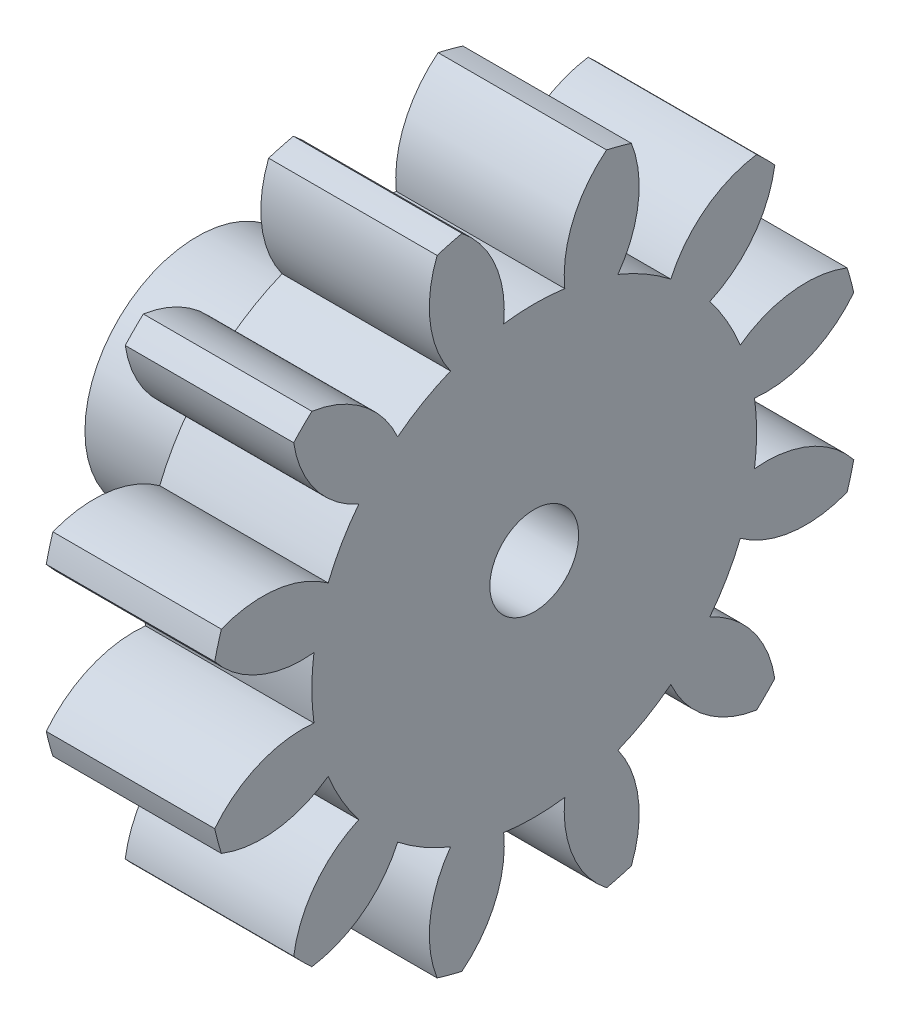
SolidWorks part; units mm, degrees
ref_plane "Plane1" through (0, 0, 0) normal (0, 0, 1) x (1, 0, 0)
ref_plane "Plane2" through (0, 0, 0) normal (0, 1, 0) x (1, 0, 0)
ref_plane "Plane3" through (0, 0, 0) normal (1, 0, 0) x (0, 0, -1)
sketch "HoldingSke" plane through (0, 0, 0) normal (0, 1, 0) x (1, 0, 0)
  line L0 (0, 0) -> (596.2788, -126.743)
  line L1 (-15, 0) -> (100, 0) construction
  line L2 (0, 0) -> (-2.1039, 2.3779)
  line L3 (0, 0) -> (-11.863, 4.5341)
  line L4 (0, 0) -> (8.4473, 1.7955)
  line L5 (0, 0) -> (-47.5972, -17.7524)
  line L6 (0, 0) -> (-3.1583, -2.1309)
  line L7 (-2.1039, 2.3779) -> (8.8308, 51.9871)
  line L8 (-76.2, 54.61) -> (-61.976, 54.61)
  line L9 (-67.7845, 28.3722) -> (-49.3413, 33.142)
  line L10 (-76.2, 71.12) -> (104.1128, 71.12)
  line L11 (0, 0) -> (-3.81, 0)
  line L12 (-76.2, 101.6) -> (-76.1573, 101.6)
  line L13 (24.9733, 27.94) -> (52.9518, 28.4284)
  line L14 (24.9733, 27.94) -> (25.0241, 27.9398)
  line L15 (24.9733, 27.94) -> (100.4021, 29.52)
  circle A0 centre (0, 0) radius 6.35
  circle A1 centre (0, 0) radius 5.0292
  circle A2 centre (0, 0) radius 38.1
  circle A3 centre (0, 0) radius 5.0038
  dimension "MHD" = 10.0584
  dimension "Hub_dia" = 76.2
  dimension "Bore" = 12.7
  dimension "MBD" = 10.0076
  dimension "Num_teeth" = 12
  dimension "Pitch" = 609.6
  dimension "Overall_len" = 50.8
  dimension "Show_teeth" = 12
  dimension "Thickness" = 3.81
  dimension "OAL" = 50.8001
  dimension "T_dim" = 14.224
  dimension "Ap" = 14.5
  dimension "H" = 19.05
  dimension "Pitch_radius" = 180.3128
  dimension "Width" = 3.81
  dimension "Backlash" = 0.0427
  dimension "Addendum_fac" = 1
  dimension "Dedendum_fac" = 1.2
  dimension "Clearance_fac" = 0.2
  dimension "Dedendum_add" = 0.0508
sketch "BasProSke" plane through (0, 0, 0) normal (0, 1, 0) x (1, 0, 0)
  line L0 (-10, 0) -> (60, 0) construction
  line L1 (0, 0) -> (0, 7.4083)
  line L2 (0, 0) -> (3.81, 0)
  line L3 (3.81, 0) -> (3.81, 7.4083)
  line L4 (3.81, 7.4083) -> (0, 7.4083)
  dimension "Thickness" = 3.81
  dimension "Diameter" = 14.8167
revolve "Base-Revolve" add sketch "BasProSke" angle 360 about L0
sketch "TooCutSke" plane through (0, 0, 0) normal (1, 0, 0) x (0, 0, -1)
  line L1 (0, 0) -> (0, 107) construction
  line L2 (0, 0) -> (-0.9034, 6.2854) construction
  line L3 (0, 0) -> (-3.2637, 12.1804) construction
  line L4 (-0.9034, 6.2854) -> (-1.6319, 6.0902) construction
  arc A0 (0.6906, 4.9816) -> (-0.6906, 4.9816) centre (0, 0) ccw
  arc A1 (1.6612, 7.2457) -> (-1.6612, 7.2457) centre (0, 0) ccw
  circle A2 centre (0, 0) radius 6.35 construction
  circle A3 centre (0, 0) radius 6.1477 construction
  arc A4 (-0.6906, 4.9816) -> (-1.6612, 7.2457) centre (-3.2176, 5.2385) ccw
  arc A5 (1.6612, 7.2457) -> (0.6906, 4.9816) centre (3.2176, 5.2385) ccw
  dimension "Root_dia" = 10.0584
  dimension "Overcut_dia" = 14.8675
  dimension "Pitch_dia" = 12.7
  dimension "Base_dia" = 12.2955
  dimension "Flank_rad" = 2.54
  dimension "Half_ang" = 15
  dimension "Half_CT" = 0.7542
extrude "ToothCut" cut sketch "TooCutSke" along normal through all
fillet "Breaks" [suppressed] radius 0.0212
fillet "RootFillets" [suppressed] radius 0.2625
pattern_circular "TeethCuts" count 12 every 30 about axis through (-10, 0, 0) along (1, 0, 0) of "ToothCut", "RootFillets", "Breaks"
sketch "HubNeaOneSke" plane through (0, 0, 0) normal (-1, 0, 0) x (0, 0, 1)
  circle A0 centre (0, 0) radius 5.0292
  dimension "Diameter" = 10.0584
extrude "HubNearOne" [suppressed] add sketch "HubNeaOneSke" along normal blind 46.9901
sketch "HubNeaBotSke" plane through (0, 0, 0) normal (-1, 0, 0) x (0, 0, 1)
  circle A0 centre (0, 0) radius 5.0292
  dimension "Diameter" = 10.0584
extrude "HubNearBoth" [suppressed] add sketch "HubNeaBotSke" along normal blind 23.495
ref_plane "FarPln" through (3.81, 0, 0) normal (1, 0, 0) x (0, 0, -1)
sketch "HubFarSke" plane through (3.81, 0, 0) normal (1, 0, 0) x (0, 0, -1)
  circle A0 centre (0, 0) radius 5.0292
  dimension "Diameter" = 10.0584
extrude "HubFar" [suppressed] add sketch "HubFarSke" along normal blind 23.495
sketch "BorSke" plane through (0, 0, 0) normal (1, 0, 0) x (0, 0, -1)
  circle A0 centre (0, 0) radius 5.0038
  dimension "Diameter" = 10.0076
extrude "Bore" cut sketch "BorSke" along normal mid plane 101.6001
sketch "KeySke" plane through (0, 0, 0) normal (1, 0, 0) x (0, 0, -1)
  line L0 (-1.5875, 0) -> (-1.5875, 9.2202)
  line L1 (-1.5875, 9.2202) -> (1.5875, 9.2202)
  line L2 (1.5875, 9.2202) -> (1.5875, 0)
  line L3 (0, 0) -> (0, 34) construction
  line L4 (-1.5875, 0) -> (1.5875, 0)
  dimension "Offset" = 9.2202
  dimension "Width" = 3.175
extrude "Keyway" [suppressed] cut sketch "KeySke" along normal mid plane 101.6001
pattern_circular "Keyway2" [suppressed] count 2 every 90 about axis through (-10, 0, 0) along (1, 0, 0)
sketch "Sketch1" plane through (0, 0, 0) normal (1, 0, 0) x (0, 0, -1)
  circle A0 centre (0, 0) radius 5.0038 construction
  circle A1 centre (0, 0) radius 5.0038
extrude "Boss-Extrude1" add sketch "Sketch1" along normal up to vertex (3.81 mm away)
sketch "Sketch2" plane through (0, 0, 0) normal (-1, 0, 0) x (0, 0, 1)
  circle A0 centre (0, 0) radius 2.54
  dimension "D1" = 5.08
extrude "Boss-Extrude2" add sketch "Sketch2" along normal blind 3.81
sketch "Sketch3" plane through (-3.81, 0, 0) normal (-1, 0, 0) x (0, 0, 1)
  circle A0 centre (0, 0) radius 1.0033
  dimension "D1" = 2.0066
extrude "Cut-Extrude1" cut sketch "Sketch3" against normal through all
equation "' \"Pitch@HoldingSke\" = 4"
equation "' \"Num_teeth@HoldingSke\" = 12"
equation "' \"Ap@HoldingSke\" =  20"
equation "' \"Ap@HoldingSke\" = 20"
equation "' \"Width@HoldingSke\" = 0.5"
equation "' \"Hub_dia@HoldingSke\"= 1"
equation "' \"Hub_dia@HoldingSke\" = 1"
equation "' \"Overall_len@HoldingSke\" = 1.0"
equation "' \"Bore@HoldingSke\" = 0.75"
equation "' \"T_dim@HoldingSke\" = 0.85"
equation "' \"Width@KeySke\" = 0.25"
equation "' \"Show_teeth@HoldingSke\" = 13"
equation "' \"Backlash@HoldingSke\" = 0.009"
equation "' \"Addendum_fac@HoldingSke\" = 1.0"
equation "' \"Dedendum_fac@HoldingSke\" = 1.25"
equation "' \"Dedendum_add@HoldingSke\" = 0.00005"
equation "' \"Clearance_fac@HoldingSke\" = 0.25"
equation "' \"Pitch@HoldingSke\" = 0.5"
equation "' \"Num_teeth@HoldingSke\" = 23"
equation "' \"Show_teeth@HoldingSke\" = 23"
equation "' \"Backlash@HoldingSke\" = 0.0375"
equation "\"Overcut_dia@TooCutSke\" = (\"Num_teeth@HoldingSke\" + 2 * \"Addendum_fac@HoldingSke\") / \"Pitch@HoldingSke\" + 0.002"
equation "\"Pitch_dia@TooCutSke\" = \"Num_teeth@HoldingSke\" / \"Pitch@HoldingSke\""
equation "\"Base_dia@TooCutSke\" = \"Num_teeth@HoldingSke\" / \"Pitch@HoldingSke\" * cos((\"Ap@HoldingSke\"  * 3.14159265 / 180))"
equation "\"Root_dia@TooCutSke\" = (\"Num_teeth@HoldingSke\" + 2) / \"Pitch@HoldingSke\" - 2 * (\"Addendum_fac@HoldingSke\" + \"Dedendum_fac@HoldingSke\") / \"Pitch@HoldingSke\" - \"Dedendum_add@HoldingSke\" * 2"
equation "\"Half_ang@TooCutSke\" = 180 / \"Num_teeth@HoldingSke\""
equation "\"Half_CT@TooCutSke\" = \"Num_teeth@HoldingSke\" / \"Pitch@HoldingSke\" * sin((3.14159265 / 2 / \"Num_teeth@HoldingSke\")) / 2 - 7 * \"Backlash@HoldingSke\" / 4"
equation "\"Flank_rad@TooCutSke\" = \"Num_teeth@HoldingSke\" / \"Pitch@HoldingSke\" / 5"
equation "\"Radius@RootFillets\" = \"Clearance_fac@HoldingSke\" / \"Pitch@HoldingSke\" + \"Dedendum_add@HoldingSke\""
equation "\"Break_rad@Breaks\" = 0.02 / \"Pitch@HoldingSke\""
equation "\"Thickness@HoldingSke\" = \"Width@HoldingSke\""
equation "\"OAL@HoldingSke\" = \"Thickness@HoldingSke\""
equation "\"MHD@HoldingSke\" = (\"Num_teeth@HoldingSke\" + 2) / \"Pitch@HoldingSke\" - 2 * (\"Addendum_fac@HoldingSke\" + \"Dedendum_fac@HoldingSke\")  / \"Pitch@HoldingSke\" - \"Dedendum_add@HoldingSke\" * 2"
equation "\"MBD@HoldingSke\" = (\"Num_teeth@HoldingSke\" + 2) / \"Pitch@HoldingSke\" - 2 * (\"Addendum_fac@HoldingSke\" + \"Dedendum_fac@HoldingSke\")  / \"Pitch@HoldingSke\" - \"Dedendum_add@HoldingSke\" * 2 - 0.002"
equation "\"MHD@HoldingSke\" = ((sgn( \"MHD@HoldingSke\" - \"Hub_dia@HoldingSke\" )-1)*( \"MHD@HoldingSke\" - \"Hub_dia@HoldingSke\" ))/-2+ \"Hub_dia@HoldingSke\""
equation "\"MBD@HoldingSke\" = ((sgn( \"MBD@HoldingSke\" - \"Bore@HoldingSke\" )-1)*( \"MBD@HoldingSke\" - \"Bore@HoldingSke\" ))/-2+ \"Bore@HoldingSke\""
equation "\"OAL@HoldingSke\" = ((sgn( \"OAL@HoldingSke\" - \"Overall_len@HoldingSke\" )+1)*( \"OAL@HoldingSke\" - \"Overall_len@HoldingSke\" ))/2 + \"Overall_len@HoldingSke\" + 0.000002"
equation "\"Num_teeth@TeethCuts\" = int( \"Show_teeth@HoldingSke\" ) + 1"
equation "\"Num_teeth@TeethCuts\" = ((sgn( \"Num_teeth@TeethCuts\" - \"Num_teeth@HoldingSke\" )-1)*( \"Num_teeth@TeethCuts\" - \"Num_teeth@HoldingSke\" ))/-2+ \"Num_teeth@HoldingSke\""
equation "\"Num_teeth@TeethCuts\" = ((sgn( \"Num_teeth@TeethCuts\" - 2.0)+1)*( \"Num_teeth@TeethCuts\" - 2.0))/2 +2.0"
equation "\"Angle@TeethCuts\" = 360.0 / \"Num_teeth@HoldingSke\""
equation "\"Diameter@BasProSke\" = (\"Num_teeth@HoldingSke\" + 2 * \"Addendum_fac@HoldingSke\") / \"Pitch@HoldingSke\""
equation "\"Thickness@BasProSke\"  = \"Thickness@HoldingSke\""
equation "' \"Fillet_rad@BasProSke\" =  \"Thickness@HoldingSke\" * 0.05"
equation "' \"Fillet_rad@BasProSke\" = \"Thickness@HoldingSke\" * 0.05"
equation "\"MHD@HoldingSke\" = ((sgn( \"MHD@HoldingSke\" - \"Root_dia@TooCutSke\" )-1)*( \"MHD@HoldingSke\" - \"Root_dia@TooCutSke\" ))/-2+ \"Root_dia@TooCutSke\""
equation "\"Diameter@HubNeaOneSke\" = \"MHD@HoldingSke\""
equation "\"Length@HubNearOne\" = \"OAL@HoldingSke\" - \"Thickness@BasProSke\""
equation "\"Diameter@HubNeaBotSke\" = \"MHD@HoldingSke\""
equation "\"Length@HubNearBoth\" = ( \"OAL@HoldingSke\" - \"Thickness@BasProSke\" ) / 2.0"
equation "\"Thickness@FarPln\" = \"Thickness@BasProSke\""
equation "\"Diameter@HubFarSke\" = \"MHD@HoldingSke\""
equation "\"Length@HubFar\" = ( \"OAL@HoldingSke\" - \"Thickness@BasProSke\" ) / 2.0"
equation "\"Diameter@BorSke\" = \"MBD@HoldingSke\""
equation "\"D1@Bore\" = \"OAL@HoldingSke\" * 2.0"
equation "\"D1@Keyway\" = \"OAL@HoldingSke\" * 2.0"
equation "\"Offset@KeySke\" = \"T_dim@HoldingSke\" - \"MBD@HoldingSke\" / 2.0"
